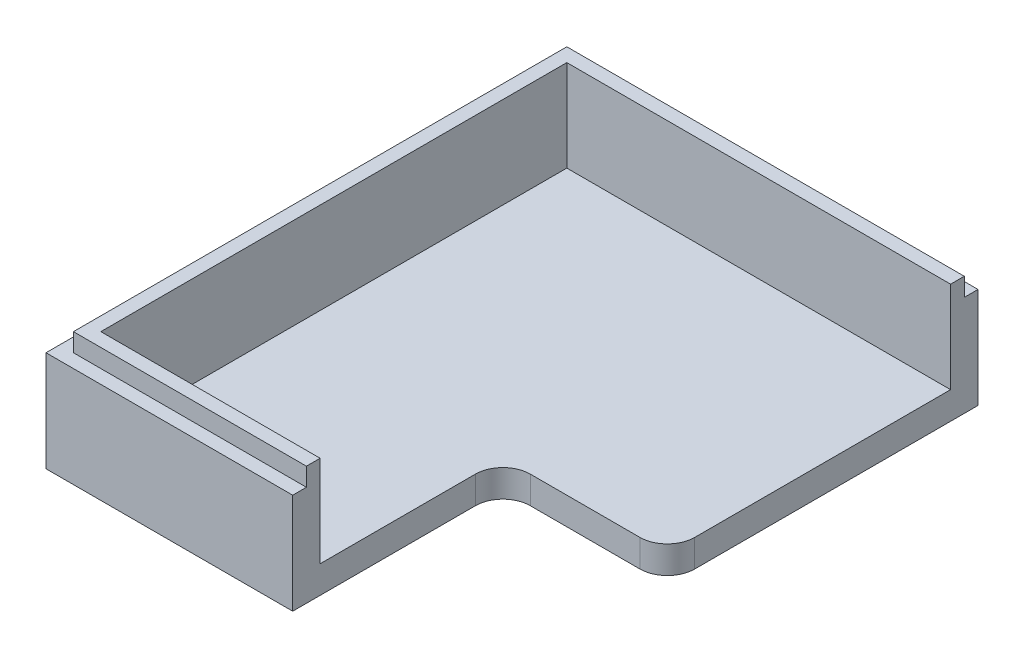
SolidWorks part; units mm, degrees
ref_plane "Plano frontal" through (0, 0, 0) normal (0, 0, 1) x (1, 0, 0)
ref_plane "Plano superior" through (0, 0, 0) normal (0, 1, 0) x (1, 0, 0)
ref_plane "Plano direito" through (0, 0, 0) normal (1, 0, 0) x (0, 0, -1)
sketch "Sketch1" plane through (0, 0, 0) normal (0, 1, 0) x (1, 0, 0)
  line L0 (32.5, 25.5) -> (-32.5, -25.5) construction
  line L1 (-32.5, 25.5) -> (32.5, 25.5) construction
  line L2 (-32.5, 25.5) -> (-32.5, -25.5) construction
  line L3 (-32.5, -25.5) -> (32.5, -25.5) construction
  line L4 (32.5, 25.5) -> (32.5, -25.5) construction
  line L5 (-35.5, 28.5) -> (35.5, 28.5)
  line L6 (35.5, 28.5) -> (35.5, -28.5)
  line L7 (-35.5, -28.5) -> (35.5, -28.5)
  line L8 (-35.5, 28.5) -> (-35.5, -28.5)
  dimension "D1" = 65
  dimension "D2" = 51
  dimension "D3" = 3
extrude "Boss-Extrude1" add sketch "Sketch1" along normal blind 3
sketch "Sketch2" plane through (0, 3, 0) normal (0, 1, 0) x (1, 0, 0)
  line L0 (-32.5, 25.5) -> (-32.5, -25.5)
  line L1 (-32.5, -25.5) -> (32.5, -25.5)
  line L2 (32.5, -25.5) -> (32.5, 25.5)
  line L3 (32.5, 25.5) -> (-32.5, 25.5)
  line L4 (-35.5, 28.5) -> (-35.5, -28.5)
  line L5 (-35.5, -28.5) -> (35.5, -28.5)
  line L6 (35.5, -28.5) -> (35.5, 28.5)
  line L7 (35.5, 28.5) -> (-35.5, 28.5)
  line L8 (-35.5, 28.5) -> (-35.5, -28.5)
  line L9 (-35.5, -28.5) -> (35.5, -28.5)
  line L10 (35.5, -28.5) -> (35.5, 28.5)
  line L11 (35.5, 28.5) -> (-35.5, 28.5)
  dimension "D1" = 0
  dimension "D2" = 3
extrude "Boss-Extrude2" add sketch "Sketch2" along normal blind 8
sketch "Sketch6" plane through (0, 11, 0) normal (0, 1, 0) x (1, 0, 0)
  line L0 (34, 27) -> (-34, 27)
  line L1 (-34, 27) -> (-34, -27)
  line L2 (-34, -27) -> (34, -27)
  line L3 (34, -27) -> (34, 27)
  line L4 (32.5, -25.5) -> (32.5, 25.5) construction
  line L5 (-32.5, -25.5) -> (32.5, -25.5) construction
  line L6 (-32.5, 25.5) -> (-32.5, -25.5) construction
  line L7 (32.5, 25.5) -> (-32.5, 25.5) construction
  line L12 (32.5, -25.5) -> (32.5, 25.5)
  line L13 (-32.5, -25.5) -> (32.5, -25.5)
  line L14 (-32.5, 25.5) -> (-32.5, -25.5)
  line L15 (32.5, 25.5) -> (-32.5, 25.5)
extrude "Boss-Extrude5" add sketch "Sketch6" along normal blind 2
sketch "Sketch7" plane through (0, 0, -28.5) normal (0, 0, -1) x (-1, 0, 0)
  line L1 (-35.5, 14.9779) -> (-9.5, 14.9779)
  line L2 (-35.5, 14.9779) -> (-35.5, -0.8518)
  line L3 (-35.5, -0.8518) -> (-9.5, -0.8518)
  line L4 (-9.5, 14.9779) -> (-9.5, -0.8518)
  dimension "D1" = 26
extrude "Cut-Extrude2" cut sketch "Sketch7" against normal through all
sketch "Sketch8" plane through (0, 0, 0) normal (0, -1, 0) x (1, 0, 0)
  line L1 (35.5, 28.5) -> (-8.5, 28.5)
  line L2 (35.5, 28.5) -> (35.5, 5.5)
  line L3 (35.5, 5.5) -> (-8.5, 5.5)
  line L4 (-8.5, 28.5) -> (-8.5, 5.5)
  line L6 (9.5, -28.5) -> (9.5, 28.5) construction
  dimension "D1" = 23
  dimension "D2" = 26
  dimension "D3" = 44
extrude "Cut-Extrude3" cut sketch "Sketch8" against normal through all
fillet "Fillet1" radius 3 2 edges at (-8.5, 1.5, 5.5) (9.5, 1.5, 5.5)
